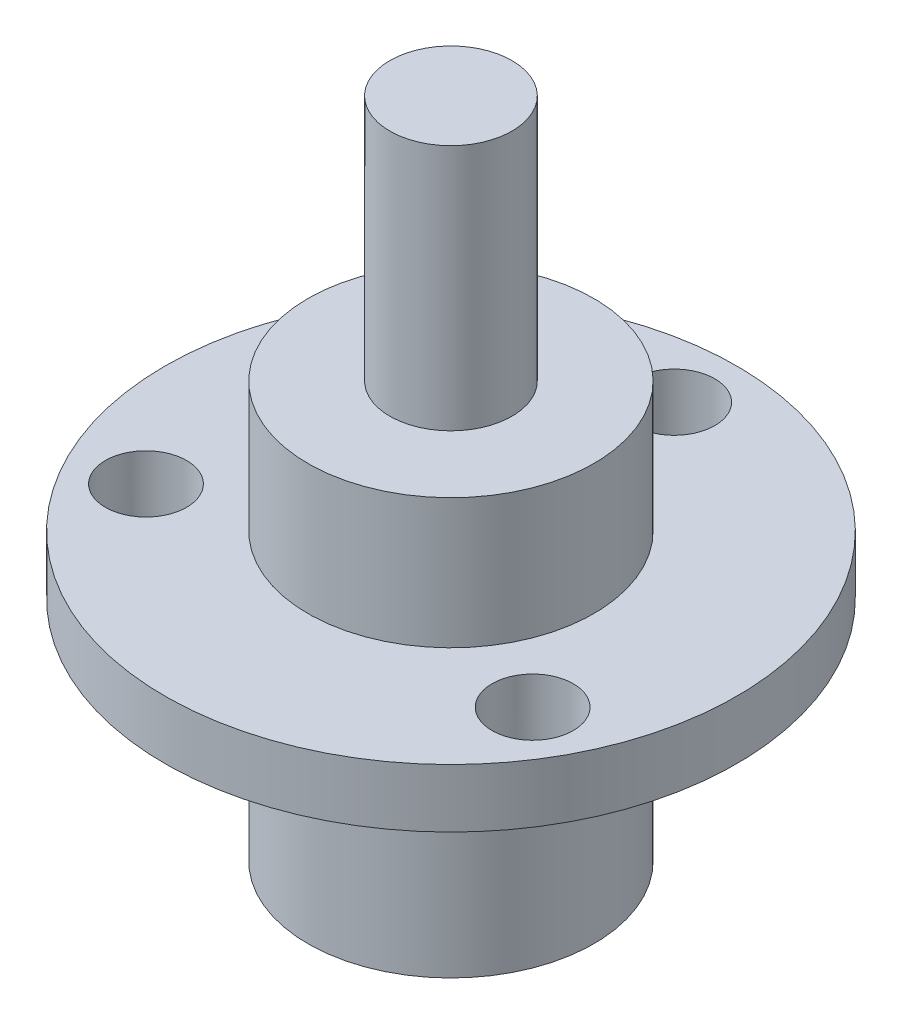
SolidWorks part; units mm, degrees
ref_plane "Front Plane" through (0, 0, 0) normal (0, 0, 1) x (1, 0, 0)
ref_plane "Top Plane" through (0, 0, 0) normal (0, 1, 0) x (1, 0, 0)
ref_plane "Right Plane" through (0, 0, 0) normal (1, 0, 0) x (0, 0, -1)
sketch "Sketch1" plane through (0, 0, 0) normal (0, 0, 1) x (1, 0, 0)
  line L0 (-5.588, 0) -> (-5.588, 8.89)
  line L1 (-5.588, 8.89) -> (-11.176, 8.89)
  line L2 (-11.176, 8.89) -> (-11.176, 11.176)
  line L3 (-11.176, 11.176) -> (-5.588, 11.176)
  line L4 (-5.588, 11.176) -> (-5.588, 16.256)
  line L5 (-5.588, 16.256) -> (-2.3876, 16.256)
  line L6 (-2.3876, 16.256) -> (-2.3876, 25.908)
  line L7 (-2.3876, 25.908) -> (0, 25.908)
  line L8 (0, 25.908) -> (0, 0)
  line L9 (0, 0) -> (-5.588, 0)
  dimension "D1" = 5.588
  dimension "D2" = 2.3876
  dimension "D3" = 2.286
  dimension "D4" = 11.176
  dimension "D5" = 11.176
  dimension "D6" = 5.08
  dimension "D7" = 14.732
revolve "Revolve1" add sketch "Sketch1" angle 360 about L8
sketch "Sketch2" plane through (0, 11.176, 0) normal (0, 1, 0) x (1, 0, 0)
  circle A0 centre (0, 0) radius 8.7249 construction
  circle A1 centre (0, 8.7249) radius 1.5875
  dimension "D1" = 17.4498
  dimension "D2" = 3.175
extrude "Cut-Extrude1" cut sketch "Sketch2" against normal through all
pattern_circular "CirPattern1" count 3 over 360 about axis through (0, 0, 0) along (0, 1, 0) of "Cut-Extrude1"
